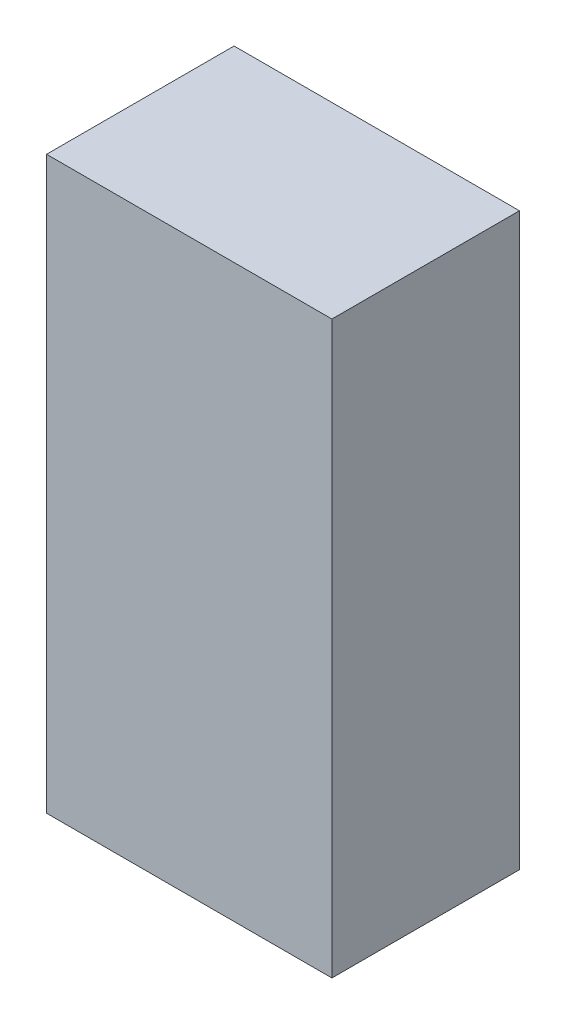
SolidWorks part; units mm, degrees
ref_plane "Front Plane" through (0, 0, 0) normal (0, 0, 1) x (1, 0, 0)
ref_plane "Top Plane" through (0, 0, 0) normal (0, 1, 0) x (1, 0, 0)
ref_plane "Right Plane" through (0, 0, 0) normal (1, 0, 0) x (0, 0, -1)
sketch "Sketch1" plane through (0, 0, 0) normal (0, 1, 0) x (1, 0, 0)
  line L1 (-17.5, -11.5) -> (17.5, -11.5)
  line L2 (-17.5, -11.5) -> (-17.5, 11.5)
  line L3 (-17.5, 11.5) -> (17.5, 11.5)
  line L4 (17.5, -11.5) -> (17.5, 11.5)
  line L5 (-17.5, -11.5) -> (17.5, 11.5) construction
  line L6 (-17.5, 11.5) -> (17.5, -11.5) construction
  point P0 (0, 0)
  dimension "D1" = 23
  dimension "D2" = 35
extrude "Boss-Extrude1" add sketch "Sketch1" along normal blind 70
